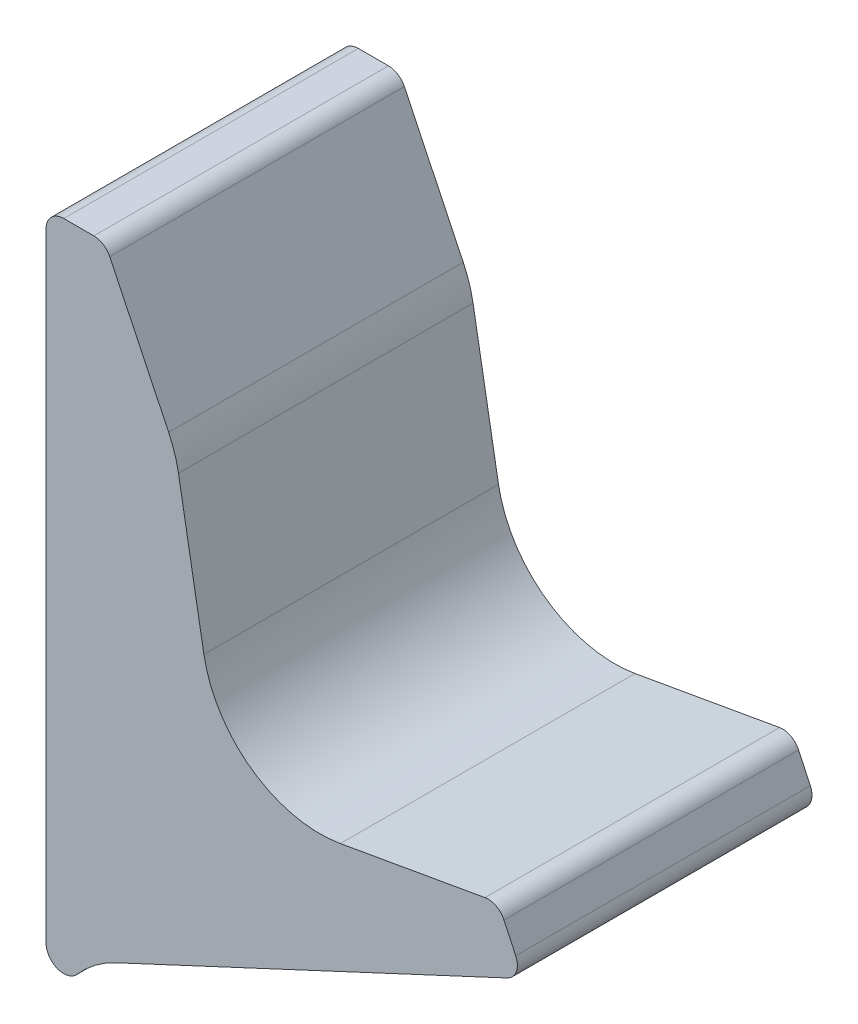
SolidWorks part; units mm, degrees
ref_plane "Plane1" through (0, 0, 0) normal (0, 0, 1) x (1, 0, 0)
ref_plane "Plane2" through (0, 0, 0) normal (0, 1, 0) x (1, 0, 0)
ref_plane "Plane3" through (0, 0, 0) normal (1, 0, 0) x (0, 0, -1)
sketch "Sketch1" plane through (0, 0, 0) normal (0, 0, 1) x (1, 0, 0)
  line L0 (0, -3) -> (0, -53.785)
  line L2 (0, -53.785) -> (0, -108)
  line L3 (11.9245, -104.9418) -> (78.2679, -74.0054)
  line L4 (79.7189, -70.0186) -> (77.7335, -65.7608)
  line L5 (74.4936, -64.0742) -> (49.9611, -68.3999)
  line L6 (26.792, -52.1767) -> (22.477, -27.7052)
  line L7 (20.8113, -22.5236) -> (10.8169, -1.7018)
  line L8 (8.1123, 0) -> (3, 0)
  arc A0 (0, -108) -> (5.2666, -109.9654) centre (3, -108) ccw
  arc A1 (5.2666, -109.9654) -> (11.9245, -104.9418) centre (20.3769, -123.068) cw
  arc A2 (49.9611, -68.3999) -> (26.792, -52.1767) centre (46.4881, -48.7038) cw
  arc A3 (78.2679, -74.0054) -> (79.7189, -70.0186) centre (77, -71.2865) ccw
  arc A4 (77.7335, -65.7608) -> (74.4936, -64.0742) centre (75.0145, -67.0286) ccw
  arc A5 (10.8169, -1.7018) -> (8.1123, 0) centre (8.1123, -3) ccw
  arc A8 (0, -3) -> (3, 0) centre (3, -3) cw
  arc A9 (22.477, -27.7052) -> (20.8113, -22.5236) centre (2.7808, -31.1782) ccw
  point P20 (76.7606, -63.6745)
  point P23 (10, 0)
  point P32 (0, 0)
  point P35 (22, -25)
  dimension "D1" = 20
  dimension "D4" = 3
  dimension "D5" = 111
  dimension "D8" = 20
  dimension "D14" = 2
  dimension "D16" = 3
  dimension "D19" = 3
  dimension "D20" = 20
  dimension "D6" = 22
  dimension "D7" = 10
  dimension "D9" = 10
  dimension "D10" = 15
  dimension "D11" = 65
  dimension "D12" = 10
  dimension "D13" = 25
  dimension "D17" = 80
extrude "Extrude1" add sketch "Sketch1" along normal mid plane 50
